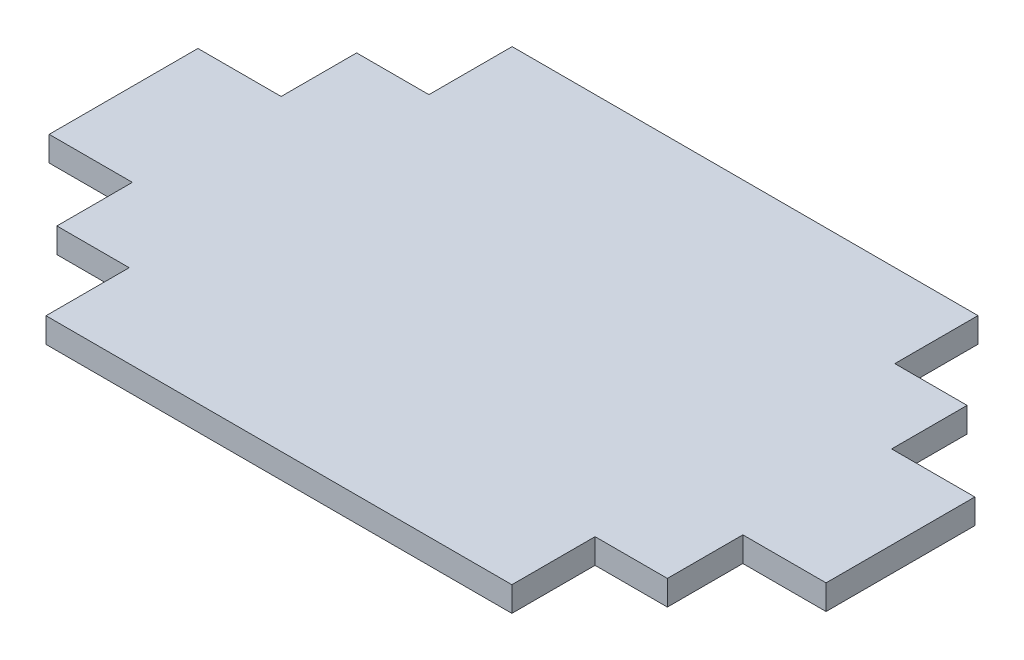
SolidWorks part; units mm, degrees
material "Acrylic (Medium-high impact)"
ref_plane "Front Plane" through (0, 0, 0) normal (0, 0, 1) x (1, 0, 0)
ref_plane "Top Plane" through (0, 0, 0) normal (0, 1, 0) x (1, 0, 0)
ref_plane "Right Plane" through (0, 0, 0) normal (1, 0, 0) x (0, 0, -1)
sketch "Sketch1" plane through (0, 0, 0) normal (0, 1, 0) x (1, 0, 0)
  line L1 (0, 0) -> (396.875, 0)
  line L2 (0, 0) -> (0, -238.125)
  line L3 (0, -238.125) -> (396.875, -238.125)
  line L4 (396.875, 0) -> (396.875, -238.125)
  dimension "D1" = 396.875
  dimension "D2" = 238.125
extrude "Boss-Extrude1" add sketch "Sketch1" along normal blind 12.7
sketch "Sketch2" plane through (0, 12.7, 0) normal (0, 1, 0) x (1, 0, 0)
  line L0 (198.4375, 0) -> (198.4375, -238.125) construction
  line L5 (396.875, 0) -> (0, 0) construction
  line L6 (0, -238.125) -> (396.875, -238.125) construction
  line L7 (0, -119.0625) -> (396.875, -119.0625) construction
  line L8 (0, 0) -> (0, -238.125) construction
  line L9 (396.875, -238.125) -> (396.875, 0) construction
  line L22 (79.4375, -238.125) -> (0, -238.125)
  line L23 (0, -81.0625) -> (42.5, -81.0625) construction
  line L24 (0, -81.0625) -> (0, -157.0625) construction
  line L25 (0, -157.0625) -> (42.5, -157.0625) construction
  line L26 (42.5, -81.0625) -> (42.5, -157.0625) construction
  line L27 (79.4375, 0) -> (317.4375, 0) construction
  line L28 (79.4375, 0) -> (79.4375, -42.5) construction
  line L29 (79.4375, -42.5) -> (317.4375, -42.5) construction
  line L30 (317.4375, 0) -> (317.4375, -42.5) construction
  line L31 (79.4375, 0) -> (0, 0)
  line L32 (79.4375, 0) -> (79.4375, -42.5)
  line L33 (79.4375, -42.5) -> (42.5, -42.5)
  line L34 (0, 0) -> (0, -42.5)
  line L35 (42.5, -81.0625) -> (0, -81.0625)
  line L36 (42.5, -81.0625) -> (42.5, -42.5)
  line L38 (0, -81.0625) -> (0, -42.5)
  line L39 (0, -238.125) -> (0, -195.625)
  line L40 (0, -157.0625) -> (0, -195.625)
  line L41 (42.5, -157.0625) -> (0, -157.0625)
  line L42 (42.5, -157.0625) -> (42.5, -195.625)
  line L43 (79.4375, -195.625) -> (42.5, -195.625)
  line L44 (79.4375, -238.125) -> (79.4375, -195.625)
  line L45 (317.4375, 0) -> (396.875, 0)
  line L46 (396.875, 0) -> (396.875, -42.5)
  line L47 (396.875, -81.0625) -> (396.875, -42.5)
  line L48 (354.375, -81.0625) -> (396.875, -81.0625)
  line L49 (354.375, -81.0625) -> (354.375, -42.5)
  line L50 (317.4375, -42.5) -> (354.375, -42.5)
  line L51 (317.4375, 0) -> (317.4375, -42.5)
  line L52 (317.4375, -238.125) -> (317.4375, -195.625)
  line L53 (317.4375, -195.625) -> (354.375, -195.625)
  line L54 (354.375, -157.0625) -> (354.375, -195.625)
  line L55 (354.375, -157.0625) -> (396.875, -157.0625)
  line L56 (396.875, -157.0625) -> (396.875, -195.625)
  line L57 (396.875, -238.125) -> (396.875, -195.625)
  line L58 (317.4375, -238.125) -> (396.875, -238.125)
  point P17 (0, -119.0625)
  point P22 (198.4375, 0)
  dimension "D1" = 76
  dimension "D2" = 42.5
  dimension "D3" = 238
  dimension "D4" = 42.5
extrude "Cut-Extrude1" cut sketch "Sketch2" against normal through all
sketch "Sketch3" plane through (0, 12.7, 0) normal (0, 1, 0) x (1, 0, 0)
  line L0 (317.4375, 0) -> (79.4375, 0) construction
  line L1 (79.1875, 0) -> (317.6875, 0) construction
  line L2 (79.1875, 0) -> (79.1875, -40) construction
  line L3 (79.1875, -40) -> (317.6875, -40) construction
  line L4 (317.6875, 0) -> (317.6875, -40) construction
  line L5 (198.4375, 0) -> (198.4375, -238.125) construction
  line L6 (79.4375, -238.125) -> (317.4375, -238.125) construction
  line L7 (396.875, -119.0625) -> (0, -119.0625) construction
  line L8 (396.875, -157.0625) -> (396.875, -81.0625) construction
  line L9 (0, -81.0625) -> (0, -157.0625) construction
  line L10 (79.1875, -238.125) -> (0, -238.125)
  line L11 (0, -132.8199) -> (40, -132.8199) construction
  line L12 (0, -132.8199) -> (0, -105.3051) construction
  line L13 (0, -105.3051) -> (40, -105.3051) construction
  line L14 (40, -132.8199) -> (40, -105.3051) construction
  line L15 (79.1875, 0) -> (0, 0)
  line L16 (79.1875, 0) -> (79.1875, -105.3051)
  line L17 (79.1875, -105.3051) -> (0, -105.3051)
  line L18 (0, 0) -> (0, -105.3051)
  line L19 (0, -238.125) -> (0, -132.8199)
  line L20 (79.1875, -132.8199) -> (0, -132.8199)
  line L21 (79.1875, -238.125) -> (79.1875, -132.8199)
  line L22 (317.6875, -238.125) -> (317.6875, -132.8199)
  line L23 (317.6875, 0) -> (317.6875, -105.3051)
  line L24 (396.875, -105.3051) -> (356.875, -105.3051) construction
  line L25 (396.875, -132.8199) -> (396.875, -105.3051) construction
  line L26 (396.875, -132.8199) -> (356.875, -132.8199) construction
  line L27 (317.6875, -132.8199) -> (396.875, -132.8199)
  line L28 (396.875, -238.125) -> (396.875, -132.8199)
  line L29 (396.875, 0) -> (396.875, -105.3051)
  line L30 (317.6875, -105.3051) -> (396.875, -105.3051)
  line L31 (317.6875, 0) -> (396.875, 0)
  line L32 (317.6875, -238.125) -> (396.875, -238.125)
  point P16 (198.4375, 0)
  point P21 (0, -119.0625)
  dimension "D1" = 238.5
  dimension "D2" = 40
  dimension "D3" = 27.5148
  dimension "D4" = 40
extrude "Cut-Extrude2" [suppressed] cut sketch "Sketch3" against normal through all
